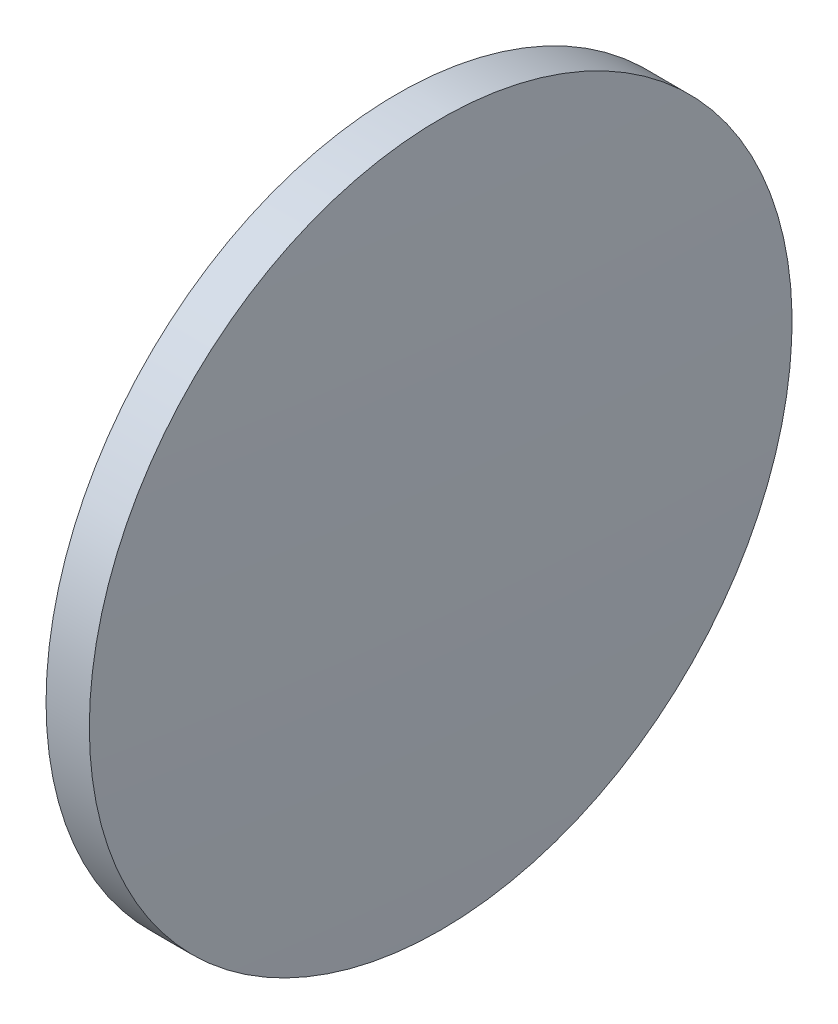
SolidWorks part; units mm, degrees
ref_plane "前视基准面" through (0, 0, 0) normal (0, 0, 1) x (1, 0, 0)
ref_plane "上视基准面" through (0, 0, 0) normal (0, 1, 0) x (1, 0, 0)
ref_plane "右视基准面" through (0, 0, 0) normal (1, 0, 0) x (0, 0, -1)
sketch "草图1" plane through (0, 0, 0) normal (0, 0, 1) x (1, 0, 0)
  line L0 (380.8972, -40.4003) -> (388.9257, -40.4003) construction
  line L1 (382.9263, -40.4003) -> (382.9263, -27.9003)
  line L2 (384.7063, -40.4003) -> (382.9263, -40.4003)
  line L5 (382.9263, -27.9003) -> (384.4663, -27.9003)
  arc A0 (384.7063, -40.4003) -> (384.4663, -27.9003) centre (59.0655, -40.4003) ccw
revolve "旋转1" add sketch "草图1" angle 360 about L0
